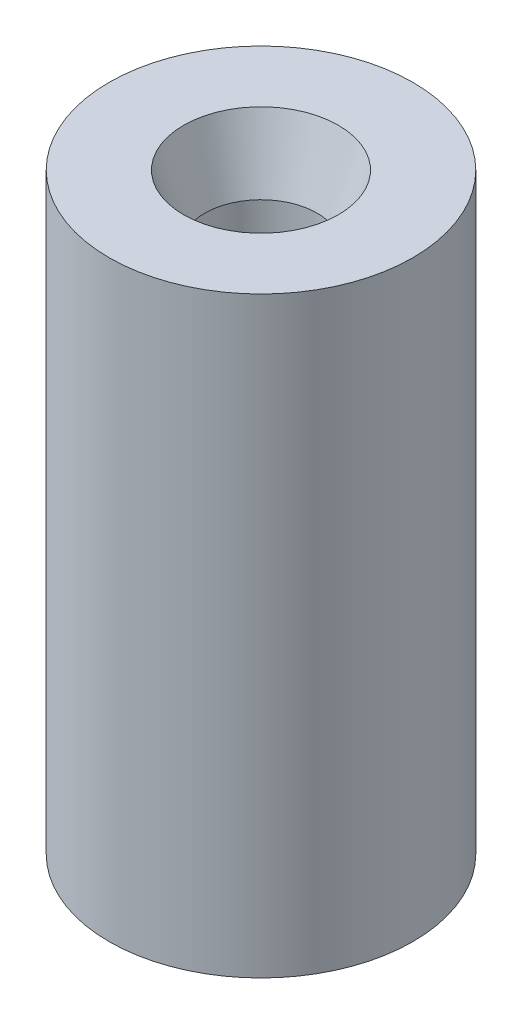
SolidWorks part; units mm, degrees
ref_plane "Front Plane" through (0, 0, 0) normal (0, 0, 1) x (1, 0, 0)
ref_plane "Top Plane" through (0, 0, 0) normal (0, 1, 0) x (1, 0, 0)
ref_plane "Right Plane" through (0, 0, 0) normal (1, 0, 0) x (0, 0, -1)
sketch "Sketch1" plane through (0, 0, 0) normal (0, 1, 0) x (1, 0, 0)
  circle A1 centre (0, 0) radius 5
  dimension "D1" = 10
extrude "Boss-Extrude1" add sketch "Sketch1" along normal blind 19.5
sketch "Sketch2" plane through (0, 19.5, 0) normal (0, 1, 0) x (1, 0, 0)
  circle A0 centre (0, 0) radius 1.85
  dimension "D1" = 3.7
extrude "Cut-Extrude1" cut sketch "Sketch2" against normal blind 26.5
chamfer "Chamfer1" distance 0.7 angle 72 2 edges at (0, 0, 1.85) (0, 19.5, 1.85)
